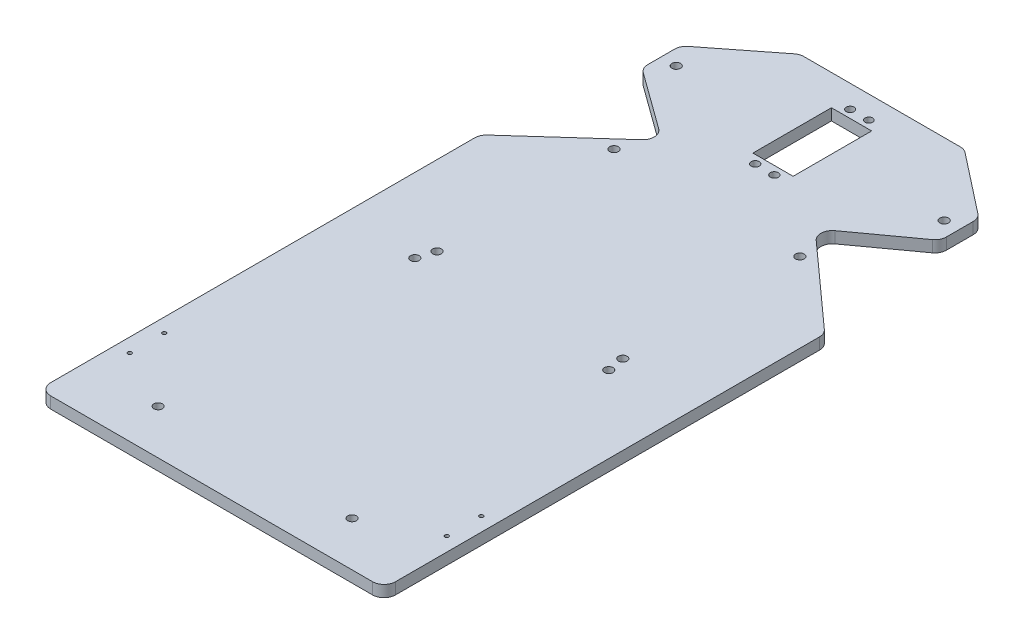
SolidWorks part; units mm, degrees
ref_plane "Alzado" through (0, 0, 0) normal (0, 0, 1) x (1, 0, 0)
ref_plane "Planta" through (0, 0, 0) normal (0, 1, 0) x (1, 0, 0)
ref_plane "Vista lateral" through (0, 0, 0) normal (1, 0, 0) x (0, 0, -1)
sketch "Croquis1" plane through (0, 0, 0) normal (0, 1, 0) x (1, 0, 0)
  line L0 (34.3727, 132.5071) -> (34.3727, -217.4929) construction
  line L1 (34.3727, 132.5071) -> (-55.6273, 132.5071) construction
  line L2 (-55.6273, -217.4929) -> (-55.6273, 12.5646)
  line L3 (-55.6273, 57.5646) -> (-5.6273, 57.5646) construction
  line L4 (77.3082, 132.5071) -> (-8.5628, 132.5071)
  line L7 (-55.6273, -217.4929) -> (124.3727, -217.4929)
  line L8 (124.3727, 57.5646) -> (74.3727, 57.5646) construction
  line L9 (124.3727, 132.5071) -> (124.3727, -217.4929) construction
  line L14 (124.3727, -217.4929) -> (124.3727, 26.1043) construction
  line L15 (-55.6273, 12.5646) -> (-55.6273, 57.5646) construction
  line L16 (-55.6273, 12.5646) -> (-5.6273, 57.5646)
  line L17 (124.3727, -217.4929) -> (124.3727, 12.5646)
  line L18 (124.3727, 12.5646) -> (74.3727, 57.5646)
  line L19 (-8.5628, 132.5071) -> (-43.5628, 105.0754)
  line L21 (-43.5628, 105.0754) -> (-43.5628, 85.0754)
  line L23 (-43.5628, 85.0754) -> (-5.6273, 57.5646)
  line L24 (77.3082, 132.5071) -> (112.3082, 105.0749)
  line L26 (112.3082, 105.0749) -> (112.3082, 85.0738)
  line L28 (112.3082, 85.0738) -> (74.3727, 57.5646)
  dimension "D1" = 350
  dimension "D2" = 90
  dimension "D3" = 50
  dimension "D4" = 75
  dimension "D5" = 45
  dimension "D6" = 77.9355
  dimension "D7" = 35
  dimension "D8" = 35
  dimension "D9" = 40
  dimension "D10" = 20
  dimension "D11" = 20.001
  dimension "D12" = 40
  dimension "D13" = 46.8609
  dimension "D14" = 46.86
  dimension "D15" = 45
  dimension "D16" = 67.2681
  dimension "D17" = 67.2681
  dimension "D18" = 77.9355
  dimension "D19" = 125.948
  dimension "D20" = 125.95
extrude "Saliente-Extruir1" add sketch "Croquis1" along normal blind 6
sketch "Croquis2" plane through (0, 6, 0) normal (0, 1, 0) x (1, 0, 0)
  line L0 (34.3727, 75.5646) -> (34.3727, 116.5646) construction
  line L1 (23.8727, 116.5646) -> (44.8727, 116.5646)
  line L2 (23.8727, 116.5646) -> (23.8727, 75.5646)
  line L3 (23.8727, 75.5646) -> (44.8727, 75.5646)
  line L4 (44.8727, 116.5646) -> (44.8727, 75.5646)
  line L6 (-5.6273, 57.5646) -> (74.3727, 57.5646) construction
  dimension "D1" = 21
  dimension "D2" = 41
  dimension "D3" = 40
extrude "Cortar-Extruir1" cut sketch "Croquis2" against normal blind 10
sketch "Croquis3" plane through (0, 6, 0) normal (0, 1, 0) x (1, 0, 0)
  line L1 (-55.6273, -217.4929) -> (124.3727, -217.4929) construction
  line L2 (34.3727, -217.4929) -> (34.3727, 132.5071) construction
  line L3 (77.3082, 132.5071) -> (-8.5628, 132.5071) construction
  line L4 (124.3727, -217.4929) -> (124.3727, 12.5646) construction
  circle A0 centre (117.1227, -177.4929) radius 1
  circle A2 centre (117.1227, -159.4929) radius 1
  circle A3 centre (-48.3773, -159.4929) radius 1
  circle A4 centre (-48.3773, -177.4929) radius 1
  dimension "D1" = 2
  dimension "D2" = 2
  dimension "D3" = 7.25
  dimension "D4" = 7.25
  dimension "D5" = 18
  dimension "D6" = 40
extrude "Cortar-Extruir2" cut sketch "Croquis3" against normal blind 10
sketch "Croquis4" plane through (0, 6, 0) normal (0, 1, 0) x (1, 0, 0)
  line L0 (-16.8773, -194.1756) -> (-16.8773, -196.4256) construction
  circle A0 centre (-16.8773, -194.1756) radius 2.25 construction
  circle A1 centre (-16.8773, -194.1756) radius 2.25
  circle A2 centre (-16.8773, -60.1756) radius 2.25
  circle A3 centre (84.3727, -60.1756) radius 2.25
  circle A4 centre (84.3727, -194.1756) radius 2.25
extrude "Cortar-Extruir3" cut sketch "Croquis4" against normal blind 10
sketch "Croquis5" plane through (0, 6, 0) normal (0, 1, 0) x (1, 0, 0)
  circle A0 centre (82.8727, -51.3456) radius 2.25
  circle A1 centre (-14.1273, -51.3456) radius 2.25
  circle A2 centre (-14.1273, 41.0744) radius 2.25
  circle A3 centre (82.8727, 41.0744) radius 2.25
  dimension "D1" = 4.5
  dimension "D2" = 4.5
  dimension "D3" = 4.5
  dimension "D4" = 4.5
extrude "Cortar-Extruir4" cut sketch "Croquis5" against normal blind 10
sketch "Croquis6" plane through (0, 0, 0) normal (0, -1, 0) x (-1, 0, 0)
  line L0 (-34.3727, 132.5071) -> (-34.3727, 54.4477) construction
  line L1 (-77.3082, 132.5071) -> (8.5628, 132.5071) construction
  line L2 (-39.2327, 120.7257) -> (-39.3627, 71.2676) construction
  line L3 (-74.3727, 57.5646) -> (5.6273, 57.5646) construction
  line L6 (-29.3827, 71.2676) -> (-29.3827, 57.5646) construction
  line L7 (-39.3627, 71.2676) -> (-39.3627, 57.5646) construction
  circle A2 centre (-29.5127, 120.6899) radius 2.0642
  circle A3 centre (-39.2327, 120.7257) radius 1.9707
  circle A7 centre (-39.3627, 71.2676) radius 2.1
  circle A8 centre (-29.3827, 71.2676) radius 2.1
  dimension "D1" = 4.86
  dimension "D2" = 4.86
  dimension "D3" = 9.72
sketch "Croquis9" plane through (0, 0, 0) normal (0, -1, 0) x (-1, 0, 0)
  line L0 (43.5628, 94.9837) -> (-112.3082, 94.9837) construction
  line L5 (-34.3727, 132.5071) -> (-34.3727, -217.4929) construction
  line L6 (-77.3082, 132.5071) -> (8.5628, 132.5071) construction
  line L7 (55.6273, -217.4929) -> (-124.3727, -217.4929) construction
  line L10 (-23.8727, 75.5646) -> (-44.8727, 75.5646) construction
  circle A0 centre (-104.3082, 94.9837) radius 2.25
  circle A1 centre (35.5628, 94.9837) radius 2.25
  point P6 (0, 0)
  point P7 (-67.3727, 95.0646)
  point P9 (0, 0)
  point P12 (-34.3727, 75.5646)
  dimension "D3" = 4.5
  dimension "D4" = 19.4192
  dimension "D1" = 8
  dimension "D2" = 19.4192
extrude "Cortar-Extruir6" cut sketch "Croquis9" against normal blind 29
extrude "Cortar-Extruir7" cut sketch "Croquis6" against normal blind 10
fillet "Redondeo1" radius 6 12 edges at (124.3727, 3, 217.4929) (-55.6273, 3, 217.4929) (-55.6273, 3, -12.5646) (124.3727, 3, -12.5646) (74.3727, 3, -57.5646) (112.3082, 3, -85.0738) (112.3082, 3, -105.0749) (77.3082, 3, -132.5071) (-5.6273, 3, -57.5646) (-43.5628, 3, -85.0754) (-43.5628, 3, -105.0754) (-8.5628, 3, -132.5071)
